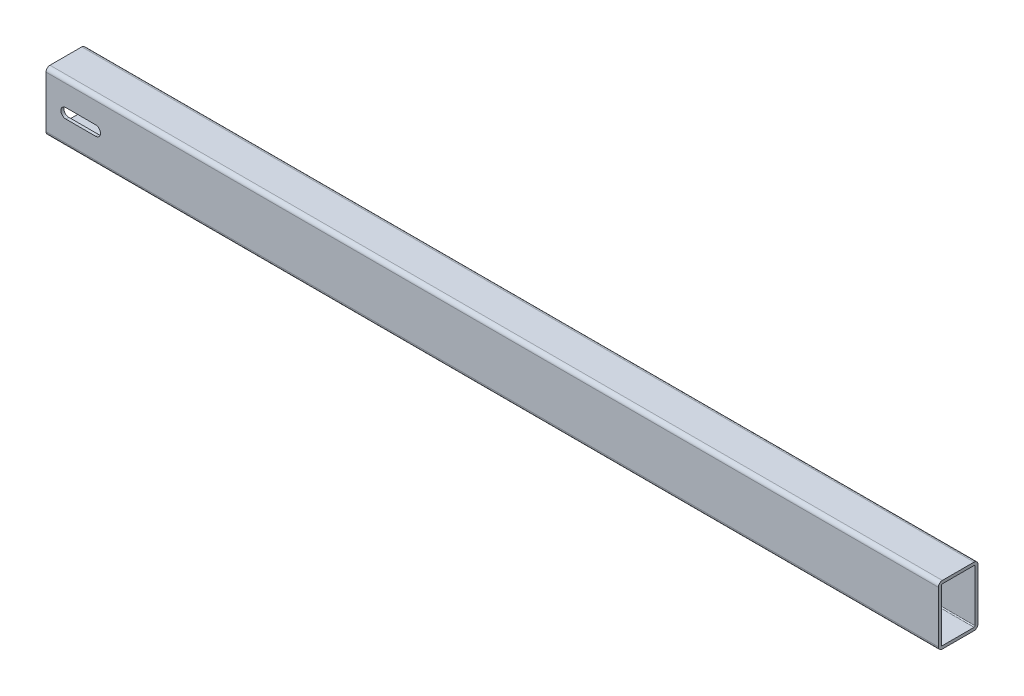
SolidWorks part; units mm, degrees
ref_plane "Спереди" through (0, 0, 0) normal (0, 0, 1) x (1, 0, 0)
ref_plane "Сверху" through (0, 0, 0) normal (0, 1, 0) x (1, 0, 0)
ref_plane "Справа" through (0, 0, 0) normal (1, 0, 0) x (0, 0, -1)
sketch "Эскиз1" plane through (0, 0, 0) normal (1, 0, 0) x (0, 0, -1)
  line L1 (1, 0) -> (33, 0)
  line L2 (0, 1) -> (0, 53)
  line L3 (1, 54) -> (33, 54)
  line L4 (34, 1) -> (34, 53)
  arc A4 (1, 0) -> (0, 1) centre (1, 1) cw
  arc A5 (33, 0) -> (34, 1) centre (33, 1) ccw
  arc A6 (34, 53) -> (33, 54) centre (33, 53) ccw
  arc A7 (0, 53) -> (1, 54) centre (1, 53) cw
  point P3 (0, 0)
  point P8 (0, 0)
  dimension "D1" = 1
extrude "Вытянуть-Тонкостенный1" add sketch "Эскиз1" along normal blind 900 thin
sketch "Эскиз2" plane through (0, 0, 3) normal (0, 0, 1) x (1, 0, 0)
  line L2 (20, 32) -> (50, 32)
  line L3 (20, 22) -> (50, 22)
  arc A0 (20, 22) -> (20, 32) centre (20, 27) cw
  arc A2 (50, 32) -> (50, 22) centre (50, 27) cw
  point P5 (0, 0)
  point P6 (0, 0)
extrude "Вырез-Вытянуть1" cut sketch "Эскиз2" against normal blind 40
